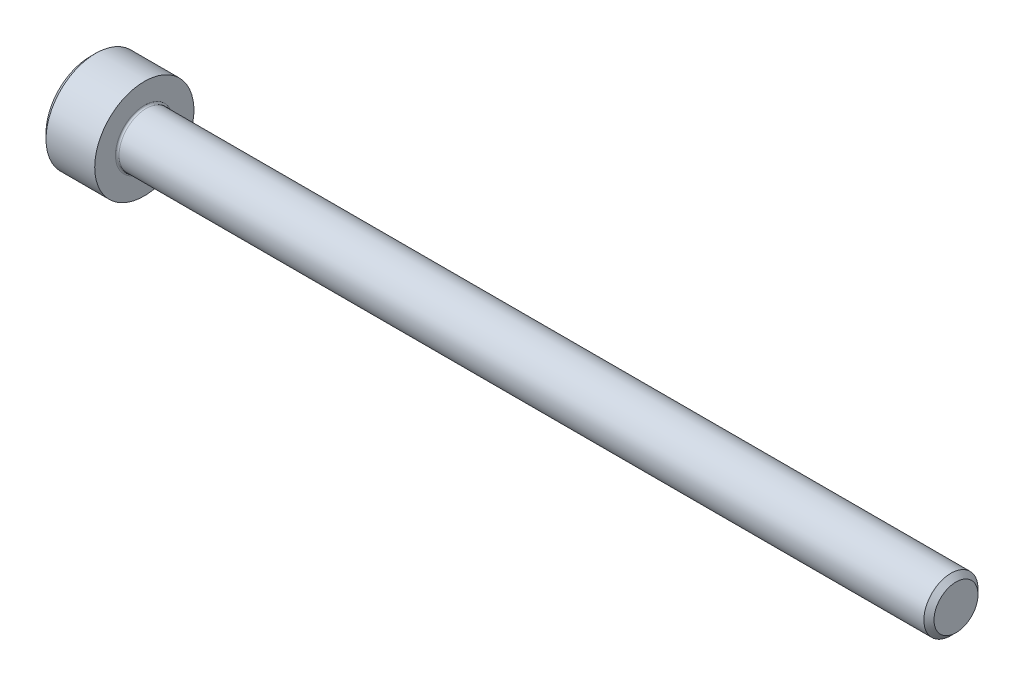
SolidWorks part; units mm, degrees
revolve "Base-Revolve" add sketch "BodySke"
sketch "BodySke" plane through (0, 0, 0) normal (0, 0, 1) x (1, 0, 0)
  line L0 (0, 0) -> (0, 2.45)
  line L1 (0.3, 2.75) -> (3, 2.75)
  line L2 (3, 2.75) -> (3, 1.5)
  line L3 (3, 1.5) -> (47.7195, 1.5)
  line L4 (48, 1.2195) -> (48, 0)
  line L5 (48, 0) -> (0, 0)
  line L6 (-31.75, 0) -> (127, 0) construction
  line L7 (0, 2.45) -> (0.3, 2.75)
  line L8 (48, 1.2195) -> (47.7195, 1.5)
  line L9 (0, -2.45) -> (0.3, -2.75) construction
  line L10 (48, -1.2195) -> (47.7195, -1.5) construction
  line L11 (3.5, 9.525) -> (3.5, 3.175) construction
  line L12 (33, 9.525) -> (33, 3.175) construction
  line L13 (-2, 9.525) -> (-2, 3.175) construction
  dimension "Diameter" = 3
  dimension "Head_ht" = 3
  dimension "Length" = 45
  dimension "Body_ch_ang" = 45
  dimension "Head_dia" = 5.5
  dimension "Head_ch_ang" = 45
  dimension "Minor_dia" = 2.439
  dimension "Advance" = 0.5
  dimension "Thread_nom" = 15
  dimension "Thread_length" = 50
  dimension "Head_ch_ht" = 0.3
cosmetic thread "ThreadCosmetic" [suppressed]
fillet "Fillet1" radius 0.1 1 edges at (3, 0, 1.5)
ref_plane "Plane1" through (0, 0, 0) normal (0, 0, 1) x (1, 0, 0)
ref_plane "Plane2" through (0, 0, 0) normal (0, 1, 0) x (1, 0, 0)
ref_plane "Plane3" through (0, 0, 0) normal (1, 0, 0) x (0, 0, -1)
sketch "Sketch2" plane through (0, 0, 0) normal (0, 0, 1) x (1, 0, 0)
  line L0 (0, 1.28) -> (1.3, 1.28)
  line L1 (1.3, 1.28) -> (2.039, 0)
  line L2 (-31.75, 0) -> (127, 0) construction
  line L3 (2.039, 0) -> (0, 0)
  line L4 (0, 0) -> (0, 1.28)
  line L5 (0, 2.45) -> (0, -2.45) construction
  line L6 (0, 0) -> (47.625, 0) construction
  line L7 (3, -2.75) -> (3, 2.75) construction
  dimension "D1" = 1.28
  dimension "D2" = 60
revolve "Hex-PreBroach" cut sketch "Sketch2" angle 360 about L6
sketch "Sketch3" plane through (0, 0, 0) normal (-1, 0, 0) x (0, 0.5, 0.866)
  line L0 (0.739, 1.28) -> (-0.739, 1.28)
  line L1 (-0.739, 1.28) -> (-1.478, 0)
  line L2 (0.739, 1.28) -> (1.478, 0)
  line L3 (0.739, -1.28) -> (1.478, 0)
  line L4 (0.739, -1.28) -> (-0.739, -1.28)
  line L5 (-0.739, -1.28) -> (-1.478, 0)
  dimension "D1" = 1.28
  dimension "D2" = 1.28
  dimension "Hex_size" = 2.56
extrude "Hex" cut sketch "Sketch3" against normal blind 1.3
sketch "Sketch4" plane through (0, 0, 0) normal (-1, 0, 0) x (0, 0, 1)
  line L0 (0, 0) -> (1.4605, 0)
  line L1 (0, 0) -> (6.1484, 3.5498) construction
  line L2 (0, 0) -> (0.7302, 1.2648)
  line L3 (1.2009, 0.3267) -> (1.3933, 0.4378)
  line L4 (0.8834, 0.8767) -> (1.0758, 0.9877)
  arc A0 (1.2009, 0.3267) -> (0.8834, 0.8767) centre (0, 0) ccw
  arc A1 (1.4605, 0) -> (1.3933, 0.4378) centre (0, 0) ccw
  arc A2 (0.7302, 1.2648) -> (1.0758, 0.9877) centre (0, 0) cw
  dimension "D1" = 30
  dimension "D2" = 60
  dimension "Spline_p_dim" = 0.635
  dimension "D3" = 0.3175
extrude "Spline" [suppressed] cut sketch "Sketch4" against normal blind 1.3
pattern_circular "CirPattern1" [suppressed] count 6 every 60
sketch "Sketch5" plane through (0, 0, 0) normal (0, 0, 1) x (1, 0, 0)
  line L0 (-31.75, 0) -> (127, 0) construction
  line L2 (0, 2.45) -> (0, -2.45) construction
  circle A0 centre (1.2, 0) radius 0.475
  dimension "Drilled_hole_dia" = 0.95
  dimension "Drilled_hole_loc" = 1.2
extrude "Hole" [suppressed] cut sketch "Sketch5" against normal through all and the other way through all
pattern_circular "Drilled-4" [suppressed] count 2 every 60
pattern_circular "Drilled-6" [suppressed] count 3 every 60
sketch "ThdSchSke" plane through (0, 0, 0) normal (0, 0, 1) x (1, 0, 0)
  line L0 (33, -1.2195) -> (32.8036, -1.5)
  line L1 (33, -1.2195) -> (33.1964, -1.5)
  line L2 (33.1964, -1.5) -> (33.1964, -1.875)
  line L3 (-3.175, 0) -> (5.1513, 0) construction
  line L5 (33.1964, -1.875) -> (32.8036, -1.875)
  line L6 (32.8036, -1.875) -> (32.8036, -1.5)
  line L7 (0, 2.45) -> (0, -2.45) construction
  dimension "Thread_minor" = 2.439
  dimension "Diameter" = 3
  dimension "Start" = 33
revolve "ThreadSchematic" [suppressed] cut sketch "ThdSchSke" angle 360 about L3
pattern_linear "ThdSchPat" [suppressed]
equation "\"D2@Sketch3\" = \"Hex_size@Sketch3\" / 2"
equation "\"D1@Sketch3\" = \"Hex_size@Sketch3\" / 2"
equation "\"D1@Sketch2\" = \"Hex_size@Sketch3\" / 2"
equation "\"D3@Sketch4\" = \"Spline_p_dim@Sketch4\" / 2"
equation "\"Thread_minor@ThreadCosmetic\"  =  \"Minor_dia@BodySke\""
equation "\"D2@CirPattern1\" = 360 / \"Num_teeth@CirPattern1\""
equation "\"Wall_thickness@Sketch2\" = \"Head_ht@BodySke\" - \"Key_eng@Hex\""
equation "\"Thread_length@ThreadCosmetic\" = ((sgn( (\"Length@BodySke\" - \"Advance@BodySke\" ) - \"Thread_nom@BodySke\" )-1)*( (\"Length@BodySke\" - \"Advance@BodySke\" ) - \"Thread_nom@BodySke\" ))/-2+ \"Thread_nom@BodySke\""
equation "\"Thread_minor@ThdSchSke\" = \"Minor_dia@BodySke\""
equation "\"Diameter@ThdSchSke\" = \"Diameter@BodySke\""
equation "\"Overcut@ThdSchSke\" = \"Diameter@BodySke\" * 1.25"
equation "\"Start@ThdSchSke\" = \"Head_ht@BodySke\" + \"Length@BodySke\" - \"Thread_length@ThreadCosmetic\"  '---Non-countersunk---"
equation "\"Num_threads@ThdSchPat\" = int( \"Thread_length@ThreadCosmetic\" / \"Advance@BodySke\" + 0.999 )  + 1"
equation "\"Advance@ThdSchPat\" = \"Thread_length@ThreadCosmetic\" /  (\"Num_threads@ThdSchPat\" - 1) 'relax it"
equation "\"Num_threads@ThdSchPat\" = \"Num_threads@ThdSchPat\" - sgn( \"Num_threads@ThdSchPat\" - 1) '---chamfered tips only---"
